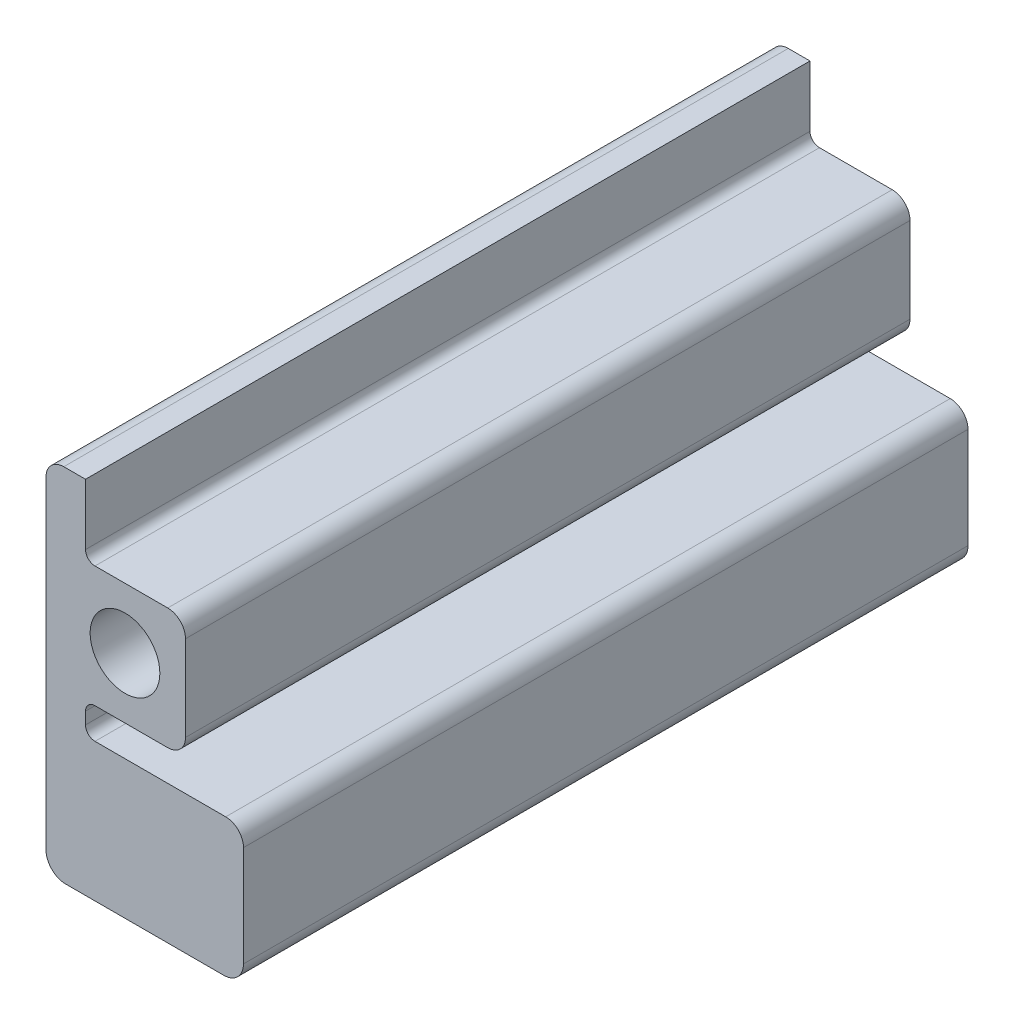
SolidWorks part; units mm, degrees
material "Pink Foam"
ref_plane "Front Plane" through (0, 0, 0) normal (0, 0, 1) x (1, 0, 0)
ref_plane "Top Plane" through (0, 0, 0) normal (0, 1, 0) x (1, 0, 0)
ref_plane "Right Plane" through (0, 0, 0) normal (1, 0, 0) x (0, 0, -1)
sketch "Sketch1" plane through (0, 0, 0) normal (0, 0, 1) x (1, 0, 0)
  line L0 (-25.4, -67.48) -> (-25.4, 36.365)
  line L2 (38.1, -67.48) -> (38.1, -35.095)
  line L3 (32.385, -29.38) -> (-9.652, -29.38)
  line L4 (-12.7, -26.332) -> (-12.7, -22.503)
  line L5 (-9.652, -19.455) -> (0, -19.455)
  line L6 (-9.652, 19.455) -> (0, 19.455)
  line L7 (-12.7, 22.503) -> (-12.7, 26.332)
  line L8 (-9.652, 29.38) -> (32.385, 29.38)
  line L9 (38.1, 35.095) -> (38.1, 36.365)
  line L10 (32.385, 42.08) -> (-19.685, 42.08)
  line L15 (0, -11.2) -> (0, -19.455) construction
  line L16 (0, 11.2) -> (0, 19.455) construction
  line L17 (11.2, 0) -> (19.455, 0) construction
  line L18 (0, 19.455) -> (13.74, 19.455)
  line L19 (19.455, 13.74) -> (19.455, 0)
  line L20 (19.455, 0) -> (19.455, -13.74)
  line L21 (13.74, -19.455) -> (0, -19.455)
  line L24 (31.75, -73.83) -> (-19.05, -73.83)
  circle A0 centre (0, 0) radius 11.2
  arc A3 (-19.685, 42.08) -> (-25.4, 36.365) centre (-19.685, 36.365) ccw
  arc A4 (38.1, 36.365) -> (32.385, 42.08) centre (32.385, 36.365) ccw
  arc A6 (32.385, 29.38) -> (38.1, 35.095) centre (32.385, 35.095) ccw
  arc A7 (38.1, -35.095) -> (32.385, -29.38) centre (32.385, -35.095) ccw
  arc A8 (19.455, -13.74) -> (13.74, -19.455) centre (13.74, -13.74) cw
  arc A9 (13.74, 19.455) -> (19.455, 13.74) centre (13.74, 13.74) cw
  arc A10 (-12.7, 26.332) -> (-9.652, 29.38) centre (-9.652, 26.332) cw
  arc A11 (-9.652, 19.455) -> (-12.7, 22.503) centre (-9.652, 22.503) cw
  arc A12 (-12.7, -22.503) -> (-9.652, -19.455) centre (-9.652, -22.503) cw
  arc A13 (-9.652, -29.38) -> (-12.7, -26.332) centre (-9.652, -26.332) cw
  arc A14 (31.75, -73.83) -> (38.1, -67.48) centre (31.75, -67.48) ccw
  arc A15 (-19.05, -73.83) -> (-25.4, -67.48) centre (-19.05, -67.48) cw
  point P12 (0, 11.2)
  point P20 (0, -11.2)
  point P22 (11.2, 0)
  point P45 (-12.7, 29.38)
  point P48 (-12.7, 19.455)
  point P53 (-12.7, -29.38)
  point P57 (38.1, -73.83)
  point P60 (38.1, -73.83)
  point P63 (-25.4, -73.83)
  dimension "D1" = 22.4
  dimension "D11" = 3.048
  dimension "D9" = 5.715
  dimension "D14" = 5.715
  dimension "D12" = 6.35
  dimension "D2" = 25.4
  dimension "D3" = 8.255
  dimension "D4" = 9.925
  dimension "D5" = 44.45
  dimension "D6" = 9.925
  dimension "D7" = 12.7
  dimension "D8" = 12.7
  dimension "D10" = 63.5
extrude "Boss-Extrude1" add sketch "Sketch1" along normal blind 232.9473
sketch "Sketch2" plane through (0, 0, 232.9473) normal (0, 0, 1) x (1, 0, 0)
  line L0 (-12.7, 22.503) -> (-12.7, 26.332) construction
  line L1 (19.455, -13.74) -> (38.1, -13.74)
  line L2 (19.455, -13.74) -> (19.455, 22.503)
  line L3 (19.455, 42.08) -> (38.1, 42.08)
  line L4 (38.1, -13.74) -> (38.1, 42.08)
  line L5 (-12.7, 22.503) -> (19.455, 22.503)
  line L6 (-12.7, 22.503) -> (-12.7, 42.08)
  line L7 (-12.7, 42.08) -> (19.455, 42.08)
  line L9 (32.385, 42.08) -> (-19.685, 42.08) construction
  line L10 (38.1, 35.095) -> (38.1, 36.365) construction
  arc A0 (-12.7, 22.503) -> (-9.652, 19.455) centre (-9.652, 22.503) ccw construction
extrude "Cut-Extrude1" cut sketch "Sketch2" against normal blind 236.982
